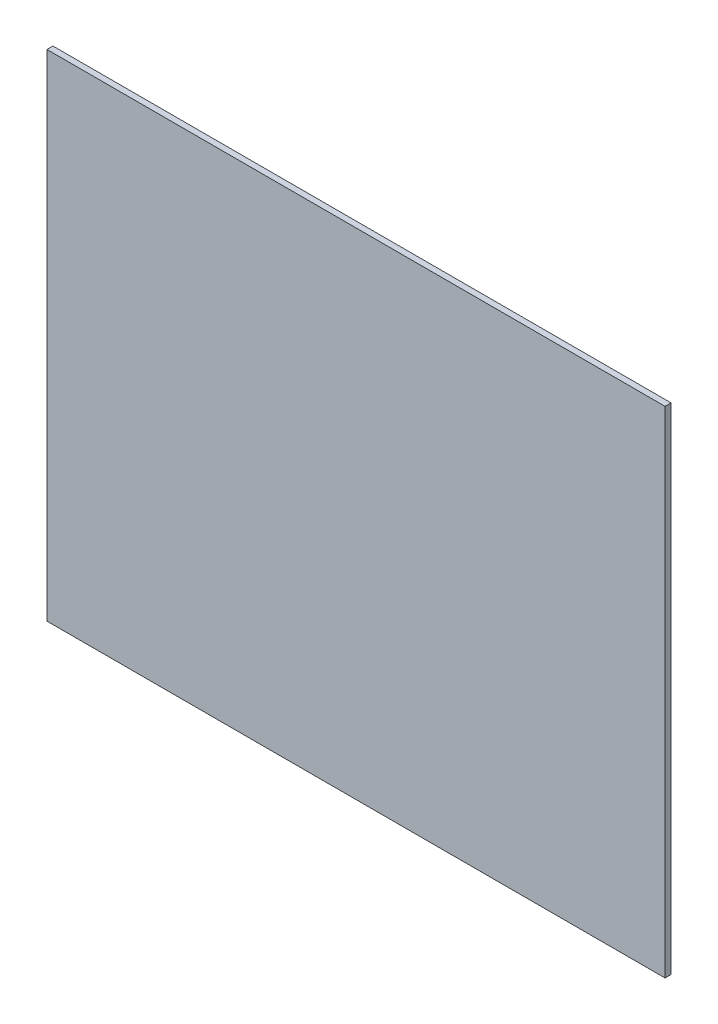
SolidWorks part; units mm, degrees
ref_plane "Alzado" through (0, 0, 0) normal (0, 0, 1) x (1, 0, 0)
ref_plane "Planta" through (0, 0, 0) normal (0, 1, 0) x (1, 0, 0)
ref_plane "Vista lateral" through (0, 0, 0) normal (1, 0, 0) x (0, 0, -1)
sketch "Croquis1" plane through (0, 0, 0) normal (0, 0, 1) x (1, 0, 0)
  line L1 (0, 0) -> (412, 0)
  line L2 (0, 0) -> (0, 330)
  line L3 (0, 330) -> (412, 330)
  line L4 (412, 0) -> (412, 330)
  dimension "D1" = 330
  dimension "D2" = 412
extrude "Saliente-Extruir1" add sketch "Croquis1" along normal blind 4
